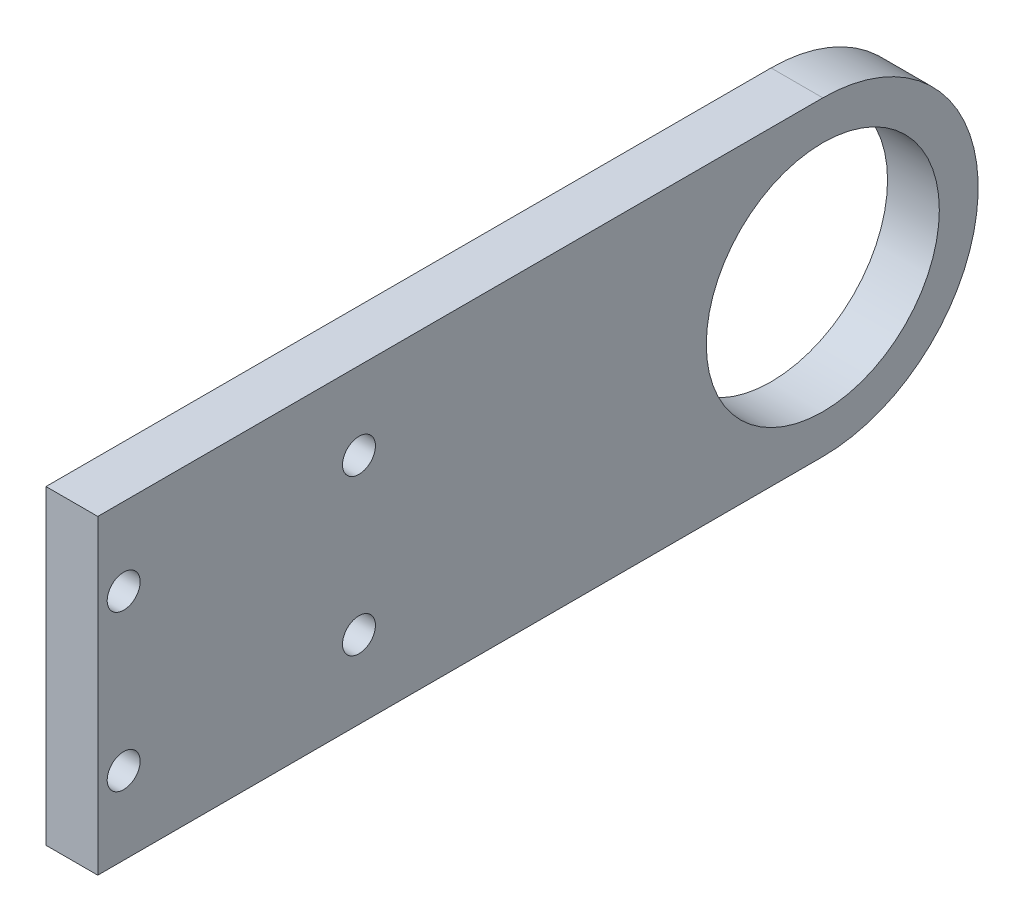
SolidWorks part; units mm, degrees
ref_plane "Front Plane" through (0, 0, 0) normal (0, 0, 1) x (1, 0, 0)
ref_plane "Top Plane" through (0, 0, 0) normal (0, 1, 0) x (1, 0, 0)
ref_plane "Right Plane" through (0, 0, 0) normal (1, 0, 0) x (0, 0, -1)
sketch "Sketch2" plane through (0, 0, 0) normal (1, 0, 0) x (0, 0, -1)
  line L0 (0, 0) -> (88.9, 0) construction
  line L2 (0, 19.05) -> (0, -19.05)
  line L5 (0, 9.525) -> (6.35, 9.525) construction
  line L6 (35.2, 9.525) -> (28.85, 9.525) construction
  line L7 (3.175, -9.525) -> (3.175, -19.05) construction
  line L8 (32.025, -9.525) -> (32.025, -19.05) construction
  line L9 (32.025, 9.525) -> (32.025, 19.05) construction
  line L10 (0, -19.05) -> (88.9, -19.05)
  line L11 (0, 19.05) -> (88.9, 19.05)
  line L13 (39.6025, -19.05) -> (24.4475, -19.05) construction
  line L14 (24.4475, -19.05) -> (32.025, -19.05) construction
  line L15 (3.175, 9.525) -> (3.175, 19.05) construction
  line L16 (0, -19.05) -> (6.35, -19.05) construction
  line L17 (6.35, -19.05) -> (3.175, -19.05) construction
  line L18 (28.85, 9.525) -> (6.35, 9.525) construction
  circle A0 centre (88.9, 0) radius 14.2875
  circle A1 centre (3.175, -9.525) radius 2.0193
  circle A2 centre (3.175, 9.525) radius 2.0193
  circle A3 centre (32.025, -9.525) radius 2.0193
  circle A4 centre (32.025, 9.525) radius 2.0193
  arc A5 (88.9, -19.05) -> (88.9, 19.05) centre (88.9, 0) ccw
  point P0 (0, 0)
  point P27 (3.175, 9.525)
  point P30 (32.025, 9.525)
  dimension "D2" = 28.575
  dimension "D3" = 3.175
  dimension "D4" = 88.9
  dimension "D5" = 4.0386
  dimension "D1" = 38.1
  dimension "D6" = 9.525
  dimension "D7" = 6.35
  dimension "D8" = 22.5
  dimension "D9" = 3.175
extrude "Boss-Extrude1" add sketch "Sketch2" along normal blind 6.35
